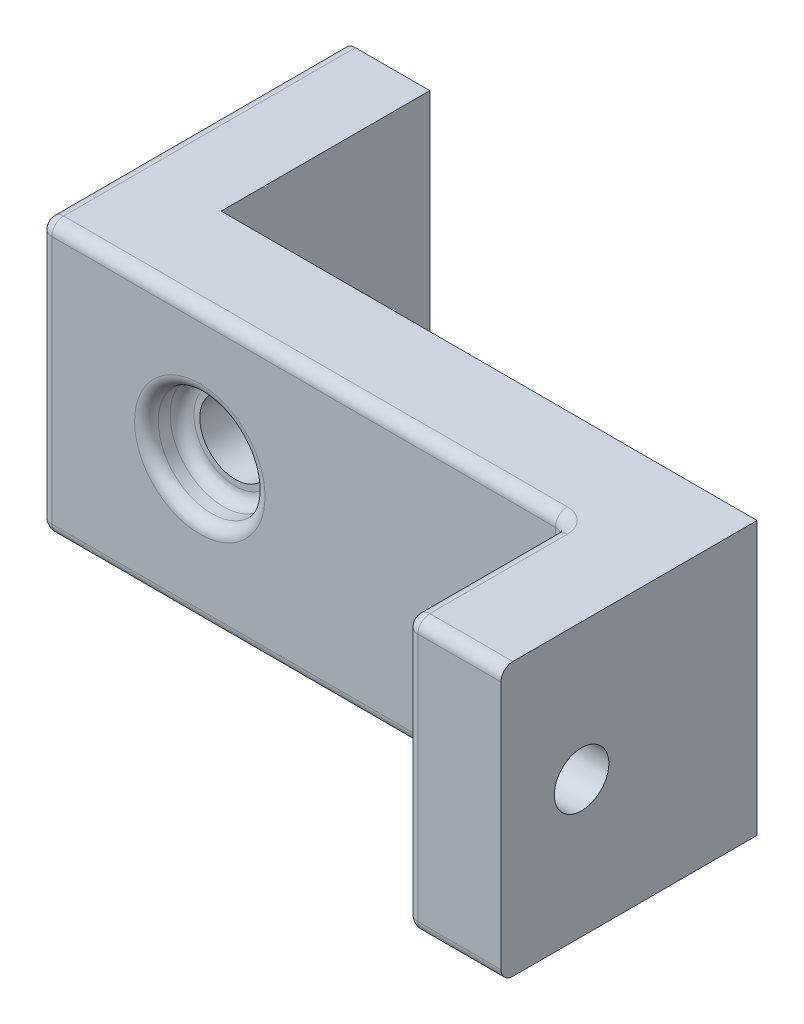
SolidWorks part; units mm, degrees
ref_plane "Front Plane" through (0, 0, 0) normal (0, 0, 1) x (1, 0, 0)
ref_plane "Top Plane" through (0, 0, 0) normal (0, 1, 0) x (1, 0, 0)
ref_plane "Right Plane" through (0, 0, 0) normal (1, 0, 0) x (0, 0, -1)
sketch "Sketch1" plane through (0, 0, 0) normal (0, 1, 0) x (1, 0, 0)
  line L0 (0, 0) -> (0, 12.8) construction
  line L1 (0, 12.8) -> (3.64, 12.8) construction
  line L2 (3.64, 12.8) -> (3.64, 4) construction
  line L3 (3.64, 4) -> (26.24, 4) construction
  line L4 (26.24, 4) -> (26.24, -6.8) construction
  line L5 (26.24, -6.8) -> (22.24, -6.8) construction
  line L6 (22.24, -6.8) -> (22.24, 0) construction
  line L7 (22.24, 0) -> (0, 0) construction
  line L8 (0, 0) -> (0, 12.8)
  line L9 (0, 12.8) -> (3.64, 12.8)
  line L10 (3.64, 12.8) -> (3.64, 4)
  line L11 (3.64, 4) -> (26.24, 4)
  line L12 (26.24, 4) -> (26.24, -6.8)
  line L13 (26.24, -6.8) -> (22.24, -6.8)
  line L14 (22.24, -6.8) -> (22.24, 0)
  line L15 (22.24, 0) -> (0, 0)
  dimension "D1" = 8.8
  dimension "D2" = 4
  dimension "D3" = 6.8
  dimension "D4" = 22.6
  dimension "D5" = 4
extrude "Boss-Extrude1" add sketch "Sketch1" along normal blind 11.5
sketch "Sketch2" plane through (0, 0, 0) normal (0, -1, 0) x (-1, 0, 0)
  line L0 (-3.64, 4) -> (-3.64, 0) construction
  line L1 (0, 0) -> (-22.24, 0) construction
  line L3 (0, 12.8) -> (0, 0) construction
sketch "Sketch3" plane through (0, 11.5, 0) normal (0, 1, 0) x (1, 0, 0)
  line L0 (3.64, 4) -> (3.64, 0) construction
  line L1 (0, 0) -> (22.24, 0) construction
  line L2 (0, 12.8) -> (0, 0) construction
sketch "Sketch4" plane through (0, 0, 0) normal (0, 0, 1) x (1, 0, 0)
  line L0 (3.64, 11.5) -> (3.64, 0) construction
  line L2 (0, 11.5) -> (22.24, 11.5) construction
  line L3 (6.74, 6) -> (22.24, 5.75) construction
  line L4 (22.24, 11.5) -> (22.24, 0) construction
  line L5 (6.74, 11.5) -> (6.74, 0) construction
  line L6 (0, 0) -> (22.24, 0) construction
  line L7 (5.24, 6) -> (5.24, 11.5) construction
  line L8 (5.24, 6) -> (5.24, 0) construction
  circle A0 centre (6.74, 6) radius 1.5 construction
  circle A1 centre (6.74, 6) radius 1.5 construction
  circle A2 centre (6.74, 6) radius 1.5
  dimension "D1" = 15.5
  dimension "D3" = 3
  dimension "D2" = 5.5
extrude "Cut-Extrude1" cut sketch "Sketch4" against normal blind 4.5
sketch "Sketch5" plane through (0, 0, 0) normal (0, 0, 1) x (1, 0, 0)
  circle A0 centre (6.74, 6) radius 2.25 construction
  circle A1 centre (6.74, 6) radius 2.25
extrude "Cut-Extrude2" cut sketch "Sketch5" against normal blind 1.5
sketch "Sketch6" plane through (22.24, 0, 0) normal (-1, 0, 0) x (0, 0, 1)
  line L0 (0, 0) -> (6.8, 11.5) construction
  line L1 (0, 11.5) -> (6.8, 0) construction
  circle A0 centre (3.4, 5.75) radius 2.15 construction
  circle A1 centre (3.4, 5.75) radius 2.15
extrude "Cut-Extrude3" cut sketch "Sketch6" against normal blind 1.75
sketch "Sketch7" plane through (23.99, 0, 0) normal (-1, 0, 0) x (0, 0, 1)
  circle A0 centre (3.4, 5.75) radius 2.15 construction
  circle A1 centre (3.4, 5.75) radius 2.15 construction
  circle A2 centre (3.4, 5.75) radius 1.15 construction
  circle A3 centre (3.4, 5.75) radius 1.15
extrude "Cut-Extrude4" cut sketch "Sketch7" against normal blind 2.5
fillet "Fillet4" radius 0.5 2 edges at (8.99, 6, -1.5) (8.99, 6, 0)
fillet "Fillet5" radius 0.5 2 edges at (22.24, 5.75, 5.55) (23.99, 5.75, 5.55)
fillet "Fillet6" radius 0.5 11 edges at (22.24, 0, 3.4) (0, 11.5, -6.4) (0, 0, -6.4) (11.12, 0, 0) (0, 5.75, 0) (22.24, 5.75, 0) (11.12, 11.5, 0) (22.24, 5.75, 6.8) (22.24, 11.5, 3.4) (24.24, 0, 6.8) (24.24, 11.5, 6.8)
